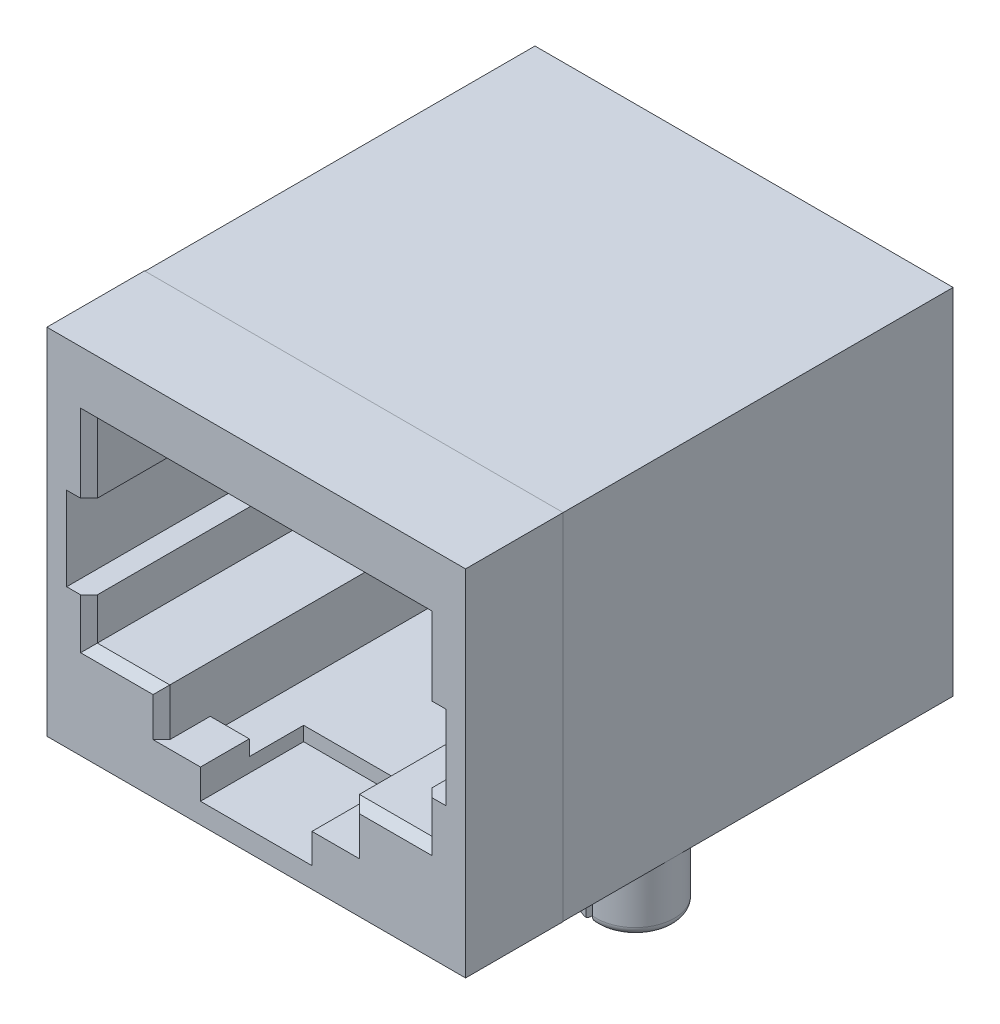
SolidWorks part; units mm, degrees
ref_plane "Front Plane" through (0, 0, 0) normal (0, 0, 1) x (1, 0, 0)
ref_plane "Top Plane" through (0, 0, 0) normal (0, 1, 0) x (1, 0, 0)
ref_plane "Right Plane" through (0, 0, 0) normal (1, 0, 0) x (0, 0, -1)
sketch "Sketch1" plane through (0, 0, 0) normal (0, 1, 0) x (1, 0, 0)
  line L1 (-7.5, 8.75) -> (7.5, 8.75)
  line L2 (-7.5, 8.75) -> (-7.5, -8.75)
  line L3 (-7.5, -8.75) -> (7.5, -8.75)
  line L4 (7.5, 8.75) -> (7.5, -8.75)
  dimension "D1" = 17.5
  dimension "D2" = 15
  dimension "D3" = 8.75
  dimension "D4" = 7.5
extrude "Extrude1" add sketch "Sketch1" along normal blind 12.7
sketch "Sketch2" plane through (0, 0, 8.75) normal (0, 0, 1) x (1, 0, 0)
  line L0 (-7.5, 12.7) -> (7.5, 12.7) construction
  line L1 (-6, 10.5) -> (6, 10.5)
  line L2 (-6, 10.5) -> (-6, 8)
  line L3 (-6, 4.5) -> (-3.4, 4.5)
  line L4 (6, 10.5) -> (6, 8)
  line L7 (3.4, 4.5) -> (6, 4.5)
  line L8 (-7.5, 12.7) -> (-7.5, 0) construction
  line L9 (-3.4, 4.5) -> (-3.4, 1.8)
  line L10 (-3.4, 1.8) -> (3.4, 1.8)
  line L11 (3.4, 4.5) -> (3.4, 1.8)
  line L12 (-6.8, 8) -> (-6, 8)
  line L13 (-6.8, 8) -> (-6.8, 5)
  line L14 (-6.8, 5) -> (-6, 5)
  line L15 (6, 5) -> (6, 4.5)
  line L16 (6, 8) -> (6.8, 8)
  line L18 (6, 5) -> (6.8, 5)
  line L19 (6.8, 8) -> (6.8, 5)
  line L20 (7.5, 12.7) -> (7.5, 0) construction
  line L21 (-6, 5) -> (-6, 4.5)
  point P19 (-7.5, 6.35)
  dimension "D1" = 12
  dimension "D2" = 6
  dimension "D3" = 6
  dimension "D4" = 2.2
  dimension "D5" = 6.8
  dimension "D6" = 3.4
  dimension "D7" = 8.7
  dimension "D8" = 0.7
  dimension "D9" = 0.7
  dimension "D10" = 3
  dimension "D11" = 0.5
extrude "Cut-Extrude1" cut sketch "Sketch2" against normal blind 11
sketch "Sketch3" plane through (0, 0, 8.75) normal (0, 0, 1) x (1, 0, 0)
  line L0 (6, 4.5) -> (6, 5) construction
  line L1 (-6, 10.5) -> (6, 10.5)
  line L2 (-6, 10.5) -> (-6, 3.5)
  line L3 (-6, 3.5) -> (6, 3.5)
  line L4 (6, 10.5) -> (6, 3.5)
  line L5 (-6, 4.5) -> (-3.4, 4.5) construction
  point P7 (-4.7, 4.5)
  dimension "D1" = 1
extrude "Cut-Extrude2" cut sketch "Sketch3" against normal blind 8.2
sketch "Sketch4" plane through (0, 0, 8.75) normal (0, 0, 1) x (1, 0, 0)
  line L0 (-3.4, 1.8) -> (3.4, 1.8) construction
  line L1 (-2, 1.8) -> (2, 1.8)
  line L2 (-2, 1.8) -> (-2, 0.7356)
  line L3 (-2, 0.7356) -> (2, 0.7356)
  line L4 (2, 1.8) -> (2, 0.7356)
  dimension "D1" = 4
  dimension "D2" = 2
extrude "Cut-Extrude3" cut sketch "Sketch4" against normal blind 3.7
ref_plane "Plane1" through (0, 0, 7) normal (0, 0, 1) x (1, 0, 0)
sketch "Sketch5" plane through (0, 0, 7) normal (0, 0, 1) x (1, 0, 0)
  line L0 (-3.4, 3.5) -> (-3.4, 1.8) construction
  line L1 (-3.4, 2.65) -> (3.4, 2.65)
  line L2 (-3.4, 2.65) -> (-3.4, 1.2462)
  line L3 (-3.4, 1.2462) -> (3.4, 1.2462)
  line L4 (3.4, 2.65) -> (3.4, 1.2462)
  line L5 (3.4, 1.8) -> (3.4, 3.5) construction
extrude "Cut-Extrude4" cut sketch "Sketch5" against normal offset from surface (10.25 mm away) 1 up to face at (0, 5.9125, -2.25) offset beyond the face yes
sketch "Sketch6" plane through (0, 0, 8.75) normal (0, 0, 1) x (1, 0, 0)
  line L1 (-6.8, 8) -> (-6, 8)
  line L2 (-6.8, 8) -> (-6.8, 5)
  line L3 (-6.8, 5) -> (-6, 5)
  line L4 (-6, 8) -> (-6, 5)
  line L5 (6, 8) -> (6.8, 8)
  line L6 (6, 8) -> (6, 5)
  line L7 (6, 5) -> (6.8, 5)
  line L8 (6.8, 8) -> (6.8, 5)
extrude "Cut-Extrude5" cut sketch "Sketch6" against normal offset from surface (12 mm away) 1 up to face at (0, 6.0188, -2.25) offset beyond the face yes
sketch "Sketch7" plane through (0, 0, 8.75) normal (0, 0, 1) x (1, 0, 0)
  line L1 (-6, 5.5) -> (6, 5.5)
  line L2 (-6, 5.5) -> (-6, 4.5)
  line L3 (-6, 4.5) -> (-3.4, 4.5)
  line L4 (6, 5.5) -> (6, 4.5)
  line L5 (3.4, 4.5) -> (6, 4.5)
  line L7 (-3.4, 4.5) -> (-3.4, 2.65)
  line L8 (-3.4, 2.65) -> (3.4, 2.65)
  line L9 (3.4, 4.5) -> (3.4, 2.65)
  dimension "D1" = 1
extrude "Cut-Extrude6" cut sketch "Sketch7" against normal offset from surface (11.5 mm away) 0.5 up to face at (0, 5.8583, -2.25) offset beyond the face yes
sketch "Sketch8" plane through (0, 0, 0) normal (0, -1, 0) x (1, 0, 0)
  line L0 (7.5, -8.75) -> (-7.5, -8.75) construction
  line L1 (-6.7, -8.75) -> (6.7, -8.75)
  line L2 (-6.7, -8.75) -> (-6.7, -2.75)
  line L3 (-6.7, -2.75) -> (6.7, -2.75)
  line L4 (6.7, -8.75) -> (6.7, -2.75)
  line L5 (3.4, -2.75) -> (-3.4, -2.75) construction
  line L6 (-7.5, -8.75) -> (-7.5, 8.75) construction
  line L7 (7.5, 8.75) -> (7.5, -8.75) construction
  dimension "D1" = 0.8
  dimension "D2" = 0.8
extrude "Cut-Extrude7" cut sketch "Sketch8" against normal offset from surface (1.7462 mm away) 0.5 up to face at (0, 1.2462, 3.95) offset beyond the face yes
chamfer "Chamfer1" distance 0.3 angle 45 9 edges at (-3.4, 2.65, 8.75) (-6, 4.25, 8.75) (-4.7, 3.5, 8.75) (3.4, 2.65, 8.75) (4.7, 3.5, 8.75) (6, 4.25, 8.75) (6, 9.25, 8.75) (0, 10.5, 8.75) (-6, 9.25, 8.75)
sketch "Sketch9" plane through (0, 0, 8.75) normal (0, 0, 1) x (1, 0, 0)
  line L0 (7.5, 12.7) -> (7.5, 0) construction
  line L1 (-7.5, 12.7) -> (7.5, 12.7) construction
  line L2 (-7.5, 12.7) -> (-7.5, 0) construction
  line L3 (7.5, 12.7) -> (7.5, 0)
  line L4 (-7.5, 12.7) -> (7.5, 12.7)
  line L5 (-7.5, 12.7) -> (-7.5, 0)
  line L6 (-7.51, 12.71) -> (-7.51, 0)
  line L7 (-7.51, 12.71) -> (7.51, 12.71)
  line L8 (7.51, 12.71) -> (7.51, 0)
  line L9 (-7.51, 0) -> (-7.5, 0)
  line L10 (7.5, 0) -> (7.51, 0)
  dimension "D1" = 0.01
extrude "Extrude2" add sketch "Sketch9" against normal blind 3.5
sketch "Sketch10" plane through (0, 0, 0) normal (0, -1, 0) x (1, 0, 0)
  line L0 (-7.51, 8.75) -> (7.51, 8.75) construction
  line L1 (-7.5, -8.75) -> (-7.5, 5.25) construction
  line L2 (7.5, 5.25) -> (7.5, -8.75) construction
  circle A0 centre (-6.1, 1.25) radius 1.4
  circle A1 centre (6.1, 1.25) radius 1.4
  dimension "D2" = 2.8
  dimension "D1" = 7.5
extrude "Extrude3" add sketch "Sketch10" along normal blind 2.2
sketch "Sketch12" plane through (0, -2.2, 0) normal (0, -1, 0) x (1, 0, 0)
  line L2 (-5.65, 2.5757) -> (-5.65, -0.0757)
  line L4 (5.65, -0.0757) -> (5.65, 2.5757)
  arc A2 (-5.65, -0.0757) -> (-5.65, 2.5757) centre (-6.1, 1.25) ccw
  arc A4 (5.65, 2.5757) -> (5.65, -0.0757) centre (6.1, 1.25) ccw
extrude "Extrude4" add sketch "Sketch12" against normal offset from surface 1.5 draft 25
sketch "Sketch11" plane through (0, 0, 0) normal (0, -1, 0) x (1, 0, 0)
  line L0 (-7.5, -8.75) -> (-7.5, 1.25) construction
  line L1 (-5.95, 3.6448) -> (-5.65, 3.6448)
  line L2 (-5.95, 3.6448) -> (-5.95, 3.1375)
  line L3 (-5.95, -0.7489) -> (-5.65, -0.7489)
  line L4 (-5.65, 2.5757) -> (-5.65, -0.0757)
  line L5 (5.65, 3.6448) -> (5.95, 3.6448)
  line L6 (5.65, 2.5757) -> (5.65, -0.0757)
  line L7 (5.65, -1.8806) -> (5.95, -1.8806)
  line L8 (5.95, 3.6448) -> (5.95, 3.5054)
  line L9 (7.5, 1.25) -> (7.5, -8.75) construction
  line L10 (-5.65, 2.5757) -> (-4.3109, 2.5757)
  line L11 (-4.3109, 2.5757) -> (-4.3109, 3.6448)
  line L12 (-4.3109, 3.6448) -> (-5.65, 3.6448)
  line L13 (-5.65, -0.0757) -> (-4.3109, -0.0757)
  line L14 (-4.3109, -0.0757) -> (-4.3109, -0.7489)
  line L15 (-4.3109, -0.7489) -> (-5.65, -0.7489)
  line L16 (5.65, 2.5757) -> (4.3928, 2.5757)
  line L17 (4.3928, 2.5757) -> (4.3928, 3.6448)
  line L18 (4.3928, 3.6448) -> (5.65, 3.6448)
  line L19 (5.65, -0.0757) -> (4.3928, -0.0757)
  line L20 (4.3928, -0.0757) -> (4.3928, -1.8806)
  line L21 (4.3928, -1.8806) -> (5.65, -1.8806)
  line L22 (-5.95, -0.6375) -> (-5.95, -0.7489)
  line L23 (-5.95, 2.6419) -> (-5.95, -0.1419)
  line L24 (5.95, 2.6419) -> (5.95, -0.1419)
  line L25 (5.95, -1.0054) -> (5.95, -1.8806)
  arc A0 (5.65, 2.5757) -> (5.65, -0.0757) centre (6.1, 1.25) ccw construction
  circle A1 centre (-6.1, 1.25) radius 1.4 construction
  arc A2 (-5.95, 2.6419) -> (-5.95, -0.1419) centre (-6.1, 1.25) ccw
  arc A3 (-5.95, 3.1375) -> (-5.95, -0.6375) centre (-6.1, 1.25) ccw
  circle A4 centre (6.1, 1.25) radius 1.4 construction
  arc A5 (5.95, -0.1419) -> (5.95, 2.6419) centre (6.1, 1.25) ccw
  arc A6 (5.95, -1.0054) -> (5.95, 3.5054) centre (6.1, 1.25) ccw
  dimension "D1" = 0.3
  dimension "D2" = 1.55
  dimension "D3" = 1.55
extrude "Cut-Extrude8" cut sketch "Sketch11" along normal through all
fillet "Fillet1" radius 0.3 4 edges at (7.5, -2.2, 1.25) (-7.5, -2.2, 1.25) (4.7, -2.2, 1.25) (-4.7, -2.2, 1.25)
ref_plane "Plane2" through (-3.7, 0, 0) normal (1, 0, 0) x (0, 0, -1)
sketch "Sketch13" plane through (-3.7, 0, 0) normal (1, 0, 0) x (0, 0, -1)
  line L0 (-6.8091, 10.5) -> (2.25, 7.4377)
  line L1 (2.25, 10.5) -> (-8.45, 10.5) construction
  line L3 (2.25, 5.5) -> (2.25, 8) construction
  line L4 (2.25, 7.4377) -> (3.966, 7.4377)
  arc A0 (-6.8091, 10.5) -> (-6.8091, 11.1274) centre (-6.7031, 10.8137) cw
ref_plane "Plane4" through (-3.7, 11.1274, 6.8091) normal (0, 0.3202, -0.9473) x (-1, 0, 0)
ref_plane "Plane5" through (3.7, 0, 0) normal (1, 0, 0) x (0, 0, -1)
sketch "Sketch16" plane through (-3.7, 0, 0) normal (1, 0, 0) x (0, 0, -1)
  line L0 (-8.75, 12.71) -> (-8.75, 0) construction
  line L1 (2.8, 11.0462) -> (-7.5, 11.0462)
  line L2 (2.8, 11.0462) -> (2.8, 7.0254)
  line L3 (2.8, 7.0254) -> (-7.5, 7.0254)
  line L4 (-7.5, 11.0462) -> (-7.5, 7.0254)
  line L5 (2.25, 10.5) -> (-8.45, 10.5) construction
  line L6 (2.25, 10.5) -> (2.25, 8) construction
  dimension "D1" = 1.25
  dimension "D2" = 0.5462
  dimension "D3" = 0.55
extrude "Cut-Extrude9" cut sketch "Sketch16" against normal blind 0.18 and the other way blind 0.18
sketch "Sketch15" plane through (-3.7, 11.1274, 6.8091) normal (0, 0.3202, -0.9473) x (-1, 0, 0)
  circle A0 centre (0, 0) radius 0.15
sweep "Sweep2" add profiles "Sketch15" path "Sketch13"
pattern_linear "LPattern1" count 8 spacing 1.05 along (1, 0, 0) of "Sweep2", "Cut-Extrude9"
ref_plane "Board Plane" through (0, -0.2, 0) normal (0, 1, 0) x (-1, 0, 0)
sketch "Component_Outline" plane through (0, -0.2, 0) normal (0, 1, 0) x (-1, 0, 0)
  line L1 (7.51, 8.75) -> (-7.5, 8.75)
  line L2 (7.51, 8.75) -> (7.51, -8.75)
  line L3 (7.51, -8.75) -> (-7.5, -8.75)
  line L4 (-7.5, 8.75) -> (-7.5, -8.75)
  point P6 (0, 0)
